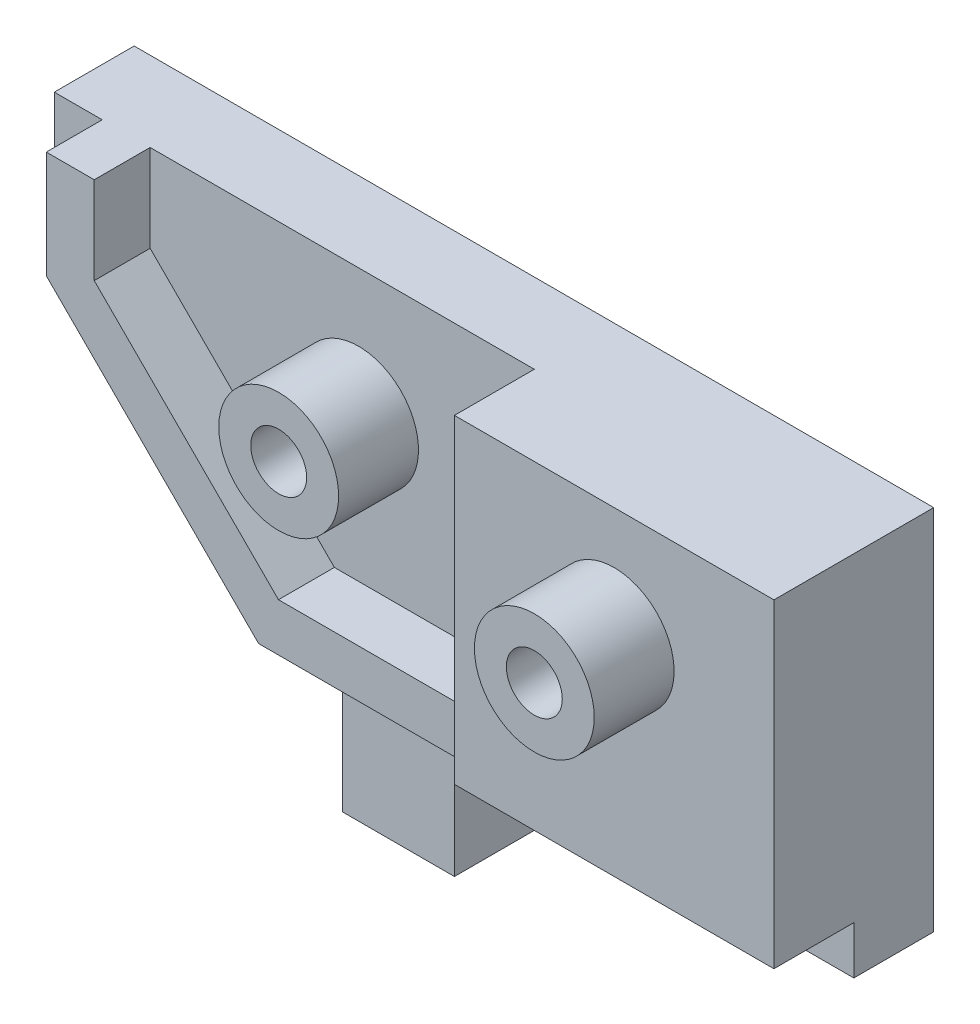
SolidWorks part; units mm, degrees
ref_plane "Front Plane" through (0, 0, 0) normal (0, 0, 1) x (1, 0, 0)
ref_plane "Top Plane" through (0, 0, 0) normal (0, 1, 0) x (1, 0, 0)
ref_plane "Right Plane" through (0, 0, 0) normal (1, 0, 0) x (0, 0, -1)
sketch "Sketch1" plane through (0, 0, 0) normal (0, 1, 0) x (1, 0, 0)
  line L0 (18, 0) -> (22, 0)
  line L1 (0, 0) -> (18, 0)
  line L2 (0, 0) -> (0, -5)
  line L3 (0, -5) -> (15, -5)
  line L4 (18, 0) -> (18, -10) construction
  line L6 (15, -5) -> (15, -10)
  line L7 (15, -10) -> (35, -10)
  line L8 (35, -5) -> (35, -10)
  line L10 (35, -5) -> (35, 0)
  line L11 (35, 0) -> (22, 0)
  dimension "D1" = 5
  dimension "D2" = 18
  dimension "D3" = 5
  dimension "D4" = 20
  dimension "D5" = 15
extrude "Boss-Extrude1" add sketch "Sketch1" along normal blind 23
sketch "Sketch2" plane through (0, 0, 10) normal (0, 0, 1) x (1, 0, 0)
  line L0 (35, 16) -> (25, 16) construction
  line L1 (35, 23) -> (35, 0) construction
  line L2 (15, 0) -> (35, 0) construction
  line L3 (0, 23) -> (0, 0) construction
  line L4 (0, 0) -> (15, 0) construction
  circle A0 centre (4, 15) radius 1.75
  circle A1 centre (25, 16) radius 1.75
  dimension "D5" = 3.5
  dimension "D6" = 3.5
  dimension "D1" = 10
  dimension "D2" = 16
  dimension "D3" = 4
  dimension "D4" = 15
extrude "Cut-Extrude1" cut sketch "Sketch2" against normal blind 10
sketch "Sketch3" plane through (0, 0, 0) normal (0, -1, 0) x (1, 0, 0)
  line L0 (0, 2.5) -> (35, 2.5) construction
  line L1 (25, 0) -> (25, 10) construction
  line L2 (35, 0) -> (0, 0) construction
  line L3 (15, 10) -> (35, 10) construction
  line L4 (0, 0) -> (0, 5) construction
  line L5 (35, 10) -> (35, 0) construction
  circle A1 centre (25, 2.5) radius 1.75
  point P1 (25, 10)
  dimension "D1" = 3.5
sketch "Sketch4" plane through (0, 0, 0) normal (0, -1, 0) x (1, 0, 0)
  line L0 (0, 2.5) -> (35, 2.5) construction
  line L1 (0, 0) -> (0, 5) construction
  line L3 (35, 10) -> (35, 0) construction
  line L7 (10, 0) -> (3, 0)
  line L8 (10, 0) -> (10, 5)
  line L9 (10, 5) -> (3, 5)
  line L10 (3, 0) -> (3, 5)
  line L11 (10, 0) -> (3, 5) construction
  line L12 (10, 5) -> (3, 0) construction
  line L17 (0, 5) -> (15, 5) construction
  point P12 (6.5, 2.5)
  dimension "D2" = 7
  dimension "D3" = 3
extrude "Boss-Extrude2" add sketch "Sketch4" along normal blind 7
sketch "Sketch6" plane through (0, 0, 5) normal (0, 0, 1) x (1, 0, 0)
  circle A0 centre (4, 15) radius 1.75
  circle A1 centre (4, 15) radius 3.75
  dimension "D1" = 2
  dimension "D2" = 3.5
extrude "Boss-Extrude3" add sketch "Sketch6" along normal blind 5
sketch "Sketch7" plane through (0, 0, 10) normal (0, 0, 1) x (1, 0, 0)
  circle A0 centre (25, 16) radius 1.75
  circle A1 centre (25, 16) radius 3.75
  dimension "D1" = 3.5
  dimension "D2" = 2
extrude "Boss-Extrude4" add sketch "Sketch7" along normal blind 5 contours A1 | A0
sketch "Sketch10" plane through (0, 0, 5) normal (0, 0, 1) x (1, 0, 0)
  line L0 (0, 23) -> (-15.0472, 23)
  line L1 (-15.0472, 15.0472) -> (0, 0)
  line L2 (0, 23) -> (0, 0) construction
  line L3 (-15.0472, 23) -> (-15.0472, 15.0472)
  line L4 (0, 23) -> (0, 0)
  dimension "D1" = 45
  dimension "D2" = 21.28
extrude "Boss-Extrude5" add sketch "Sketch10" against normal blind 5
sketch "Sketch11" plane through (0, 0, 5) normal (0, 0, 1) x (1, 0, 0)
  line L0 (-12.0472, 23) -> (-12.0472, 16.2899)
  line L1 (-15.0472, 23) -> (15, 23) construction
  line L2 (-12.0472, 16.2899) -> (1.2426, 3)
  line L3 (1.2426, 3) -> (15, 3)
  line L4 (15, 23) -> (15, 0) construction
  line L5 (-15.0472, 23) -> (-15.0472, 15.0472) construction
  line L6 (-15.0472, 15.0472) -> (0, 0) construction
  line L7 (0, 0) -> (3, 0) construction
  line L8 (-9.0472, 23) -> (-9.0472, 17.5325)
  line L9 (-9.0472, 17.5325) -> (2.4853, 6)
  line L10 (2.4853, 6) -> (15, 6)
  line L11 (-12.0472, 23) -> (-9.0472, 23)
  line L12 (15, 6) -> (15, 3)
  dimension "D1" = 3
  dimension "D2" = 3
  dimension "D3" = 3
  dimension "D4" = 3
extrude "Boss-Extrude6" add sketch "Sketch11" along normal blind 3.5
extrude "Cut-Extrude2" cut sketch "Sketch3" against normal blind 10 contours A1
sketch "Sketch12" plane through (15, 0, 0) normal (-1, 0, 0) x (0, 0, 1)
  line L1 (5, 3) -> (10, 3)
  line L2 (5, 3) -> (5, 0)
  line L3 (5, 0) -> (10, 0)
  line L4 (10, 3) -> (10, 0)
extrude "Cut-Extrude3" cut sketch "Sketch12" against normal up to surface (20 mm away) up to face at (35, 11.5, 5)
